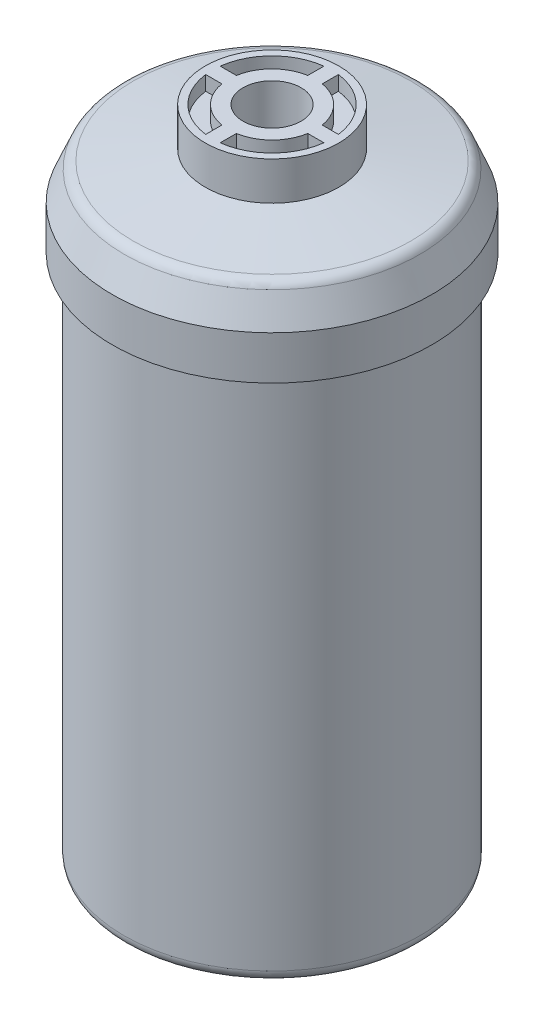
SolidWorks part; units mm, degrees
ref_plane "Front Plane" through (0, 0, 0) normal (0, 0, 1) x (1, 0, 0)
ref_plane "Top Plane" through (0, 0, 0) normal (0, 1, 0) x (1, 0, 0)
ref_plane "Right Plane" through (0, 0, 0) normal (1, 0, 0) x (0, 0, -1)
sketch "Sketch1" plane through (0, 0, 0) normal (0, 0, 1) x (1, 0, 0)
  line L1 (6.35, 154.305) -> (14.605, 154.305)
  line L2 (14.605, 154.305) -> (14.605, 145.923)
  line L3 (14.605, 145.923) -> (30.3298, 143.5934)
  line L5 (32.385, 124.968) -> (32.385, 13.1249)
  line L6 (30.2042, 10.6105) -> (14.605, 8.382)
  line L7 (14.605, 8.382) -> (14.605, 0)
  line L8 (14.605, 0) -> (6.35, 0)
  line L9 (32.3022, 142.0577) -> (34.925, 135.763)
  line L10 (34.925, 135.763) -> (34.925, 126.238)
  line L11 (34.925, 126.238) -> (32.385, 124.968)
  line L12 (6.35, 0) -> (6.35, 10.4099)
  line L13 (6.35, 10.4099) -> (29.21, 13.6757)
  line L14 (29.21, 13.6757) -> (29.21, 140.5496)
  line L15 (29.21, 140.5496) -> (6.35, 143.9363)
  line L16 (6.35, 143.9363) -> (6.35, 154.305)
  line L17 (0, 0) -> (0, 154.305) construction
  arc A0 (32.385, 13.1249) -> (30.2042, 10.6105) centre (29.845, 13.1249) cw
  arc A1 (30.3298, 143.5934) -> (32.3022, 142.0577) centre (29.9576, 141.0808) cw
  point P16 (0, 0)
  point P17 (0, 0)
  point P18 (0, 0)
  point P19 (0, 0)
  point P24 (32.385, 10.922)
  point P27 (31.75, 143.383)
  dimension "D14" = 2.54
  dimension "D3" = 154.305
  dimension "D4" = 12.7
  dimension "D5" = 10.3687
  dimension "D6" = 8.382
  dimension "D7" = 29.21
  dimension "D8" = 9.525
  dimension "D9" = 2.54
  dimension "D10" = 7.62
  dimension "D11" = 1.27
  dimension "D12" = 8.382
  dimension "D13" = 2.54
  dimension "D15" = 34.925
  dimension "D16" = 8.255
  dimension "D17" = 8.255
  dimension "D18" = 3.175
  dimension "D19" = 3.175
  dimension "D20" = 3.175
revolve "Revolve1" add sketch "Sketch1" angle 360 about L17
sketch "Sketch2" plane through (0, 0, 0) normal (0, -1, 0) x (1, 0, 0)
  line L0 (1.5875, -12.9203) -> (1.5875, -9.3918)
  line L1 (12.9203, -1.5875) -> (9.3918, -1.5875)
  line L2 (-1.5875, -12.9203) -> (-1.5875, -9.3918)
  line L3 (-12.9203, -1.5875) -> (-9.3918, -1.5875)
  line L4 (-12.9203, 1.5875) -> (-9.3918, 1.5875)
  line L5 (-1.5875, 12.9203) -> (-1.5875, 9.3918)
  line L6 (1.5875, 12.9203) -> (1.5875, 9.3918)
  line L7 (12.9203, 1.5875) -> (9.3918, 1.5875)
  arc A0 (1.5875, -9.3918) -> (9.3918, -1.5875) centre (0, 0) ccw
  arc A1 (1.5875, -12.9203) -> (12.9203, -1.5875) centre (0, 0) ccw
  circle A2 centre (0, 0) radius 14.605 construction
  circle A3 centre (0, 0) radius 6.35 construction
  arc A4 (-9.3918, -1.5875) -> (-1.5875, -9.3918) centre (0, 0) ccw
  arc A5 (-12.9203, -1.5875) -> (-1.5875, -12.9203) centre (0, 0) ccw
  arc A6 (-1.5875, 9.3918) -> (-9.3918, 1.5875) centre (0, 0) ccw
  arc A7 (-1.5875, 12.9203) -> (-12.9203, 1.5875) centre (0, 0) ccw
  arc A8 (9.3918, 1.5875) -> (1.5875, 9.3918) centre (0, 0) ccw
  arc A9 (12.9203, 1.5875) -> (1.5875, 12.9203) centre (0, 0) ccw
  point P25 (0, 0)
  dimension "D1" = 1.5875
  dimension "D2" = 3.175
  dimension "D3" = 1.5875
  dimension "D4" = 1.5875
  dimension "D5" = 4
extrude "Cut-Extrude2" cut sketch "Sketch2" against normal blind 3.175
sketch "Sketch3" plane through (0, 154.305, 0) normal (0, 1, 0) x (-1, 0, 0)
  line L0 (1.5875, -12.9203) -> (1.5875, -9.3918)
  line L1 (12.9203, -1.5875) -> (9.3918, -1.5875)
  line L2 (-1.5875, -12.9203) -> (-1.5875, -9.3918)
  line L3 (-12.9203, -1.5875) -> (-9.3918, -1.5875)
  line L4 (-12.9203, 1.5875) -> (-9.3918, 1.5875)
  line L5 (-1.5875, 12.9203) -> (-1.5875, 9.3918)
  line L6 (1.5875, 12.9203) -> (1.5875, 9.3918)
  line L7 (12.9203, 1.5875) -> (9.3918, 1.5875)
  arc A0 (1.5875, -9.3918) -> (9.3918, -1.5875) centre (0, 0) ccw
  arc A1 (1.5875, -12.9203) -> (12.9203, -1.5875) centre (0, 0) ccw
  arc A4 (-9.3918, -1.5875) -> (-1.5875, -9.3918) centre (0, 0) ccw
  arc A5 (-12.9203, -1.5875) -> (-1.5875, -12.9203) centre (0, 0) ccw
  arc A6 (-1.5875, 9.3918) -> (-9.3918, 1.5875) centre (0, 0) ccw
  arc A7 (-1.5875, 12.9203) -> (-12.9203, 1.5875) centre (0, 0) ccw
  arc A8 (9.3918, 1.5875) -> (1.5875, 9.3918) centre (0, 0) ccw
  arc A9 (12.9203, 1.5875) -> (1.5875, 12.9203) centre (0, 0) ccw
  point P25 (0, 0)
  dimension "D1" = 13.0175
  dimension "D2" = 9.525
  dimension "D3" = 1.5875
  dimension "D4" = 1.5875
  dimension "D5" = 4
extrude "Cut-Extrude3" cut sketch "Sketch3" against normal blind 3.175
